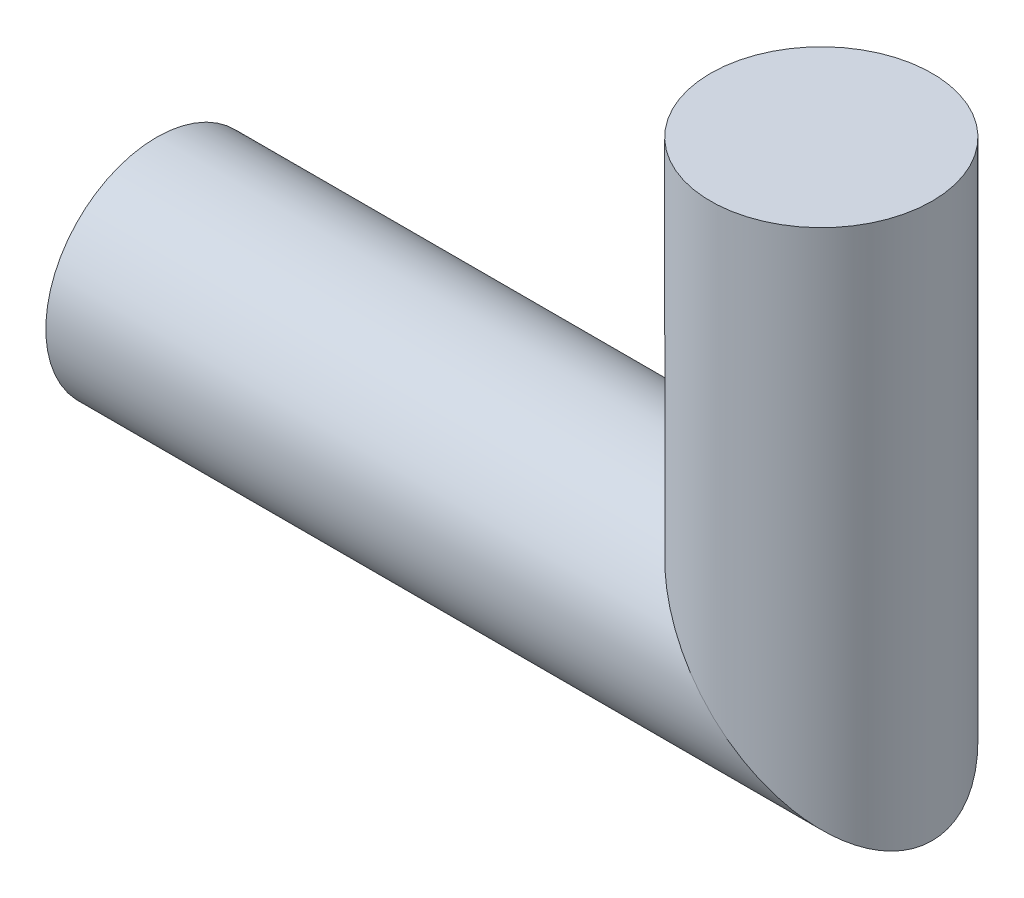
SolidWorks part; units mm, degrees
material "Acrylic (Medium-high impact)"
ref_plane "Front Plane" through (0, 0, 0) normal (0, 0, 1) x (1, 0, 0)
ref_plane "Top Plane" through (0, 0, 0) normal (0, 1, 0) x (1, 0, 0)
ref_plane "Right Plane" through (0, 0, 0) normal (1, 0, 0) x (0, 0, -1)
sketch "Sketch2" plane through (0, 0, 0) normal (0, 0, 1) x (1, 0, 0)
  line L0 (0, 0) -> (0, 101.6)
  line L1 (0, 0) -> (-152.4, 0)
  dimension "D1" = 101.6
  dimension "D2" = 152.4
sweep "Sweep1" add path "Sketch2" circular profile diameter 50.8 parameters "D3"=50.8
sketch "Sketch9" plane through (-152.4, 0, 0) normal (-1, 0, 0) x (0, 0, 1)
  circle A0 centre (0, 0) radius 12.7
  dimension "D1" = 25.4
extrude "Cut-Extrude1" cut sketch "Sketch9" against normal blind 25.4
